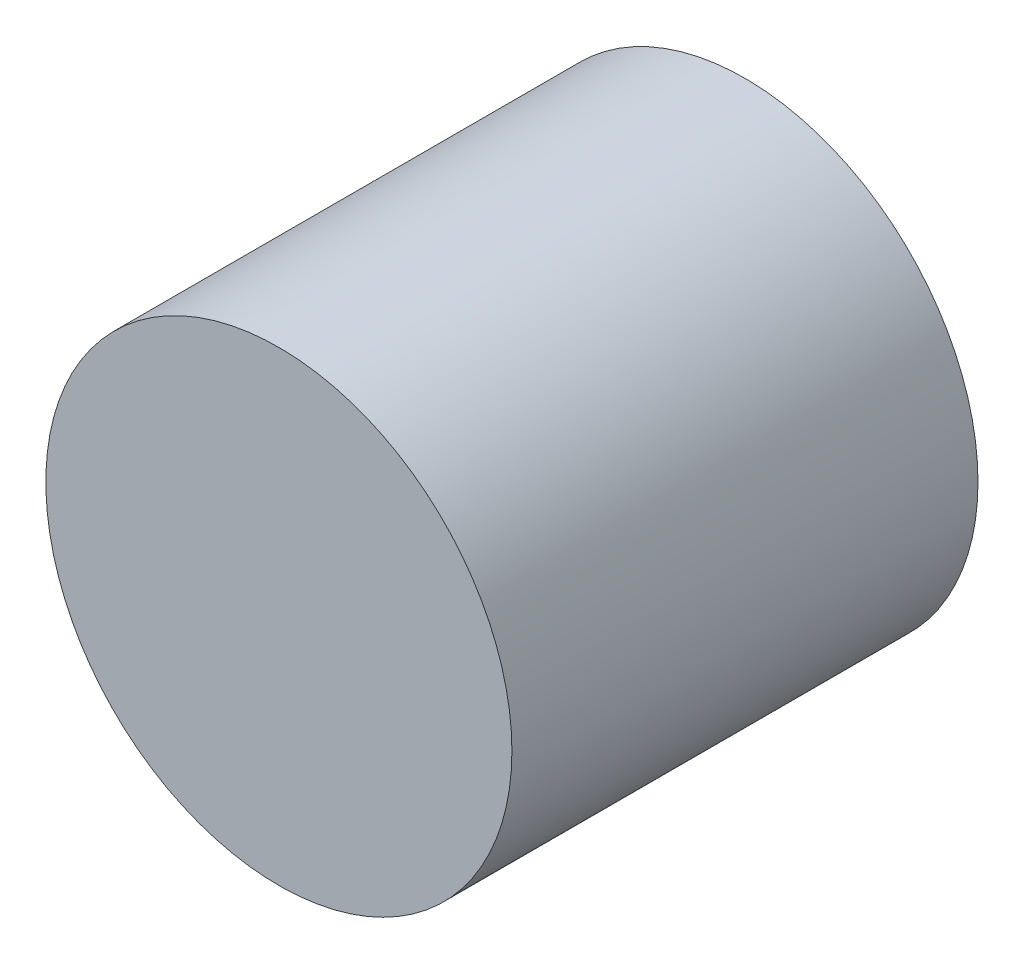
SolidWorks part; units mm, degrees
ref_plane "Plan de face" through (0, 0, 0) normal (0, 0, 1) x (1, 0, 0)
ref_plane "Plan de dessus" through (0, 0, 0) normal (0, 1, 0) x (1, 0, 0)
ref_plane "Plan de droite" through (0, 0, 0) normal (1, 0, 0) x (0, 0, -1)
sketch "Esquisse1" plane through (0, 0, 0) normal (0, 0, 1) x (1, 0, 0)
  circle A0 centre (0, 0) radius 50
  dimension "D1" = 100
extrude "Boss.-Extru.1" add sketch "Esquisse1" along normal blind 100
